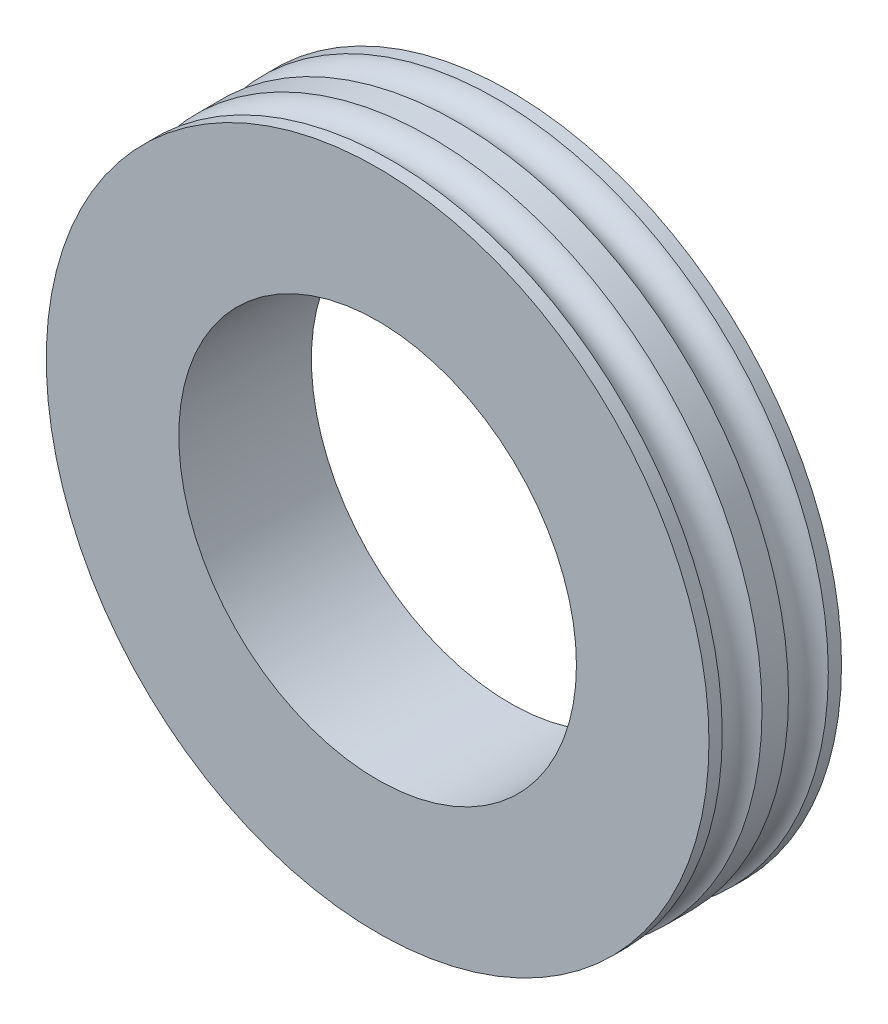
SolidWorks part; units mm, degrees
ref_plane "Front Plane" through (0, 0, 0) normal (0, 0, 1) x (1, 0, 0)
ref_plane "Top Plane" through (0, 0, 0) normal (0, 1, 0) x (1, 0, 0)
ref_plane "Right Plane" through (0, 0, 0) normal (1, 0, 0) x (0, 0, -1)
sketch "Sketch2" plane through (0, 0, 0) normal (1, 0, 0) x (0, 0, -1)
  line L0 (0, 3) -> (0, 5)
  line L1 (0, 5) -> (-0.2, 5)
  line L2 (-1, 5) -> (-1, 3)
  line L4 (-1, 3) -> (0, 3)
  line L5 (-3.0147, 0) -> (3.0268, 0) construction
  line L6 (-0.8, 5) -> (-1, 5)
  arc A0 (-0.8, 5) -> (-0.2, 5) centre (-0.5, 5.1) ccw
  dimension "D6" = 0.1
  dimension "D1" = 3
  dimension "D2" = 1
  dimension "D3" = 5
  dimension "D4" = 0.2
  dimension "D5" = 0.2
revolve "Revolve1" add sketch "Sketch2" angle 360 about L5
ref_plane "Plane1" through (0, 0, 0) normal (0, 0, -1) x (-1, 0, 0)
mirror "Mirror2" about plane through (0, 0, 0) normal (0, 0, -1) of "Revolve1"
